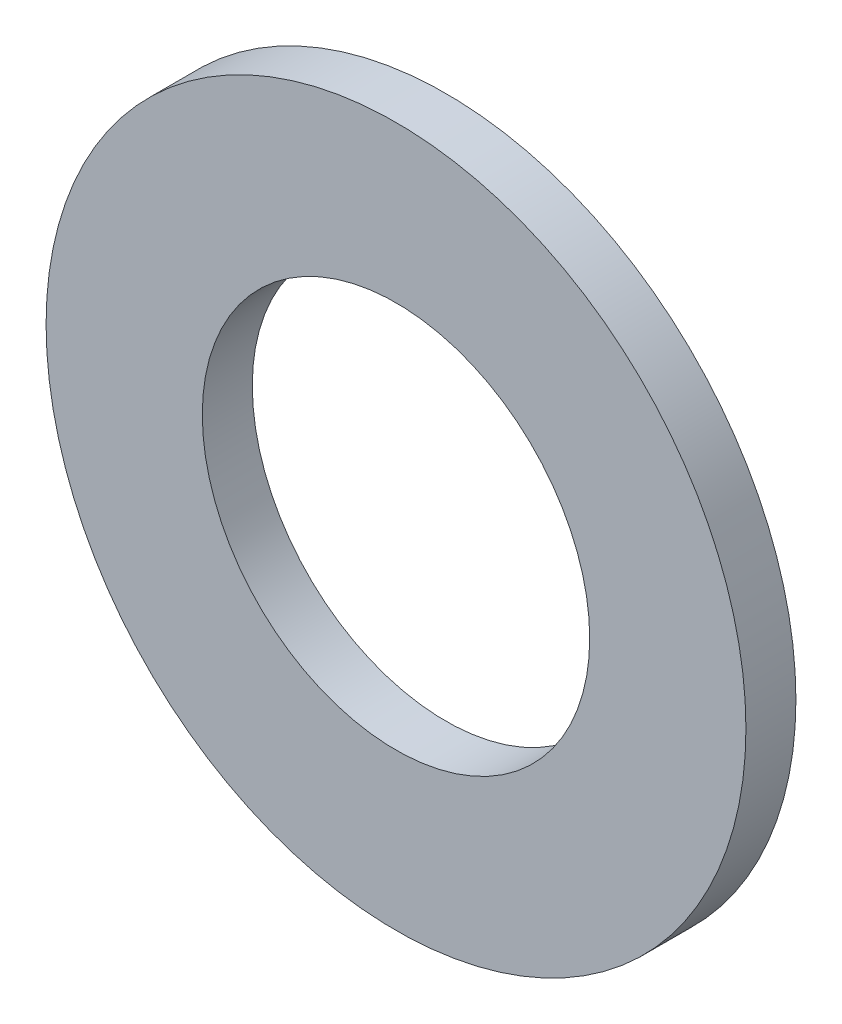
SolidWorks part; units mm, degrees
ref_plane "Płaszczyzna XY" through (0, 0, 0) normal (0, 0, 1) x (1, 0, 0)
ref_plane "Płaszczyzna XZ" through (0, 0, 0) normal (0, 1, 0) x (1, 0, 0)
ref_plane "Płaszczyzna YZ" through (0, 0, 0) normal (1, 0, 0) x (0, 0, -1)
sketch "Szkic1" plane through (0, 0, 0) normal (0, 0, 1) x (1, 0, 0)
  circle A0 centre (0, 0) radius 15.5
  circle A1 centre (0, 0) radius 28
  dimension "D1" = 31
  dimension "D2" = 56
extrude "Dodanie-wyciągnięcie1" add sketch "Szkic1" along normal blind 4
